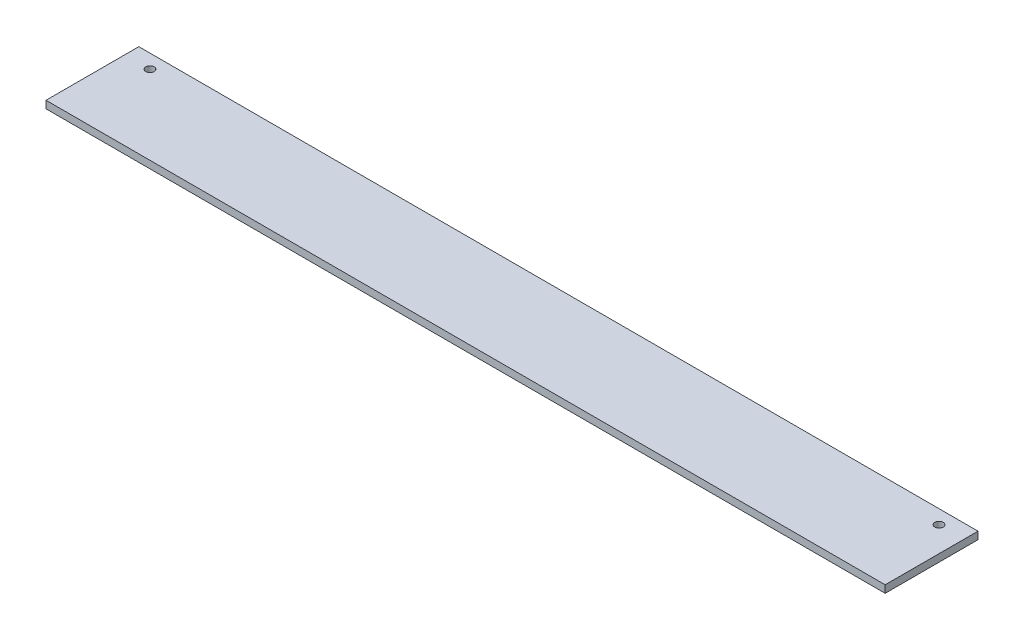
SolidWorks part; units mm, degrees
ref_plane "Спереди" through (0, 0, 0) normal (0, 0, 1) x (1, 0, 0)
ref_plane "Сверху" through (0, 0, 0) normal (0, 1, 0) x (1, 0, 0)
ref_plane "Справа" through (0, 0, 0) normal (1, 0, 0) x (0, 0, -1)
sketch "Эскиз1" plane through (0, 0, 0) normal (1, 0, 0) x (0, 0, -1)
  line L1 (-25, -2) -> (25, -2)
  line L2 (-25, -2) -> (-25, 2)
  line L3 (-25, 2) -> (25, 2)
  line L4 (25, -2) -> (25, 2)
  line L5 (-25, -2) -> (25, 2) construction
  line L6 (-25, 2) -> (25, -2) construction
  point P0 (0, 0)
  dimension "D1" = 4
  dimension "D2" = 50
extrude "Бобышка-Вытянуть1" add sketch "Эскиз1" along normal blind 452
sketch "Эскиз2" plane through (0, 2, 0) normal (0, 1, 0) x (1, 0, 0)
  line L0 (452, 25) -> (0, 25) construction
  line L1 (0, 25) -> (0, -25) construction
  line L2 (452, 25) -> (452, -25) construction
  circle A0 centre (13.5, 17.5) radius 2.25
  circle A1 centre (438.5, 17.5) radius 2.25
  dimension "D1" = 4.5
  dimension "D4" = 4.5
  dimension "D2" = 7.5
  dimension "D3" = 13.5
  dimension "D5" = 13.5
  dimension "D6" = 7.5
extrude "Вырез-Вытянуть1" cut sketch "Эскиз2" against normal through all
